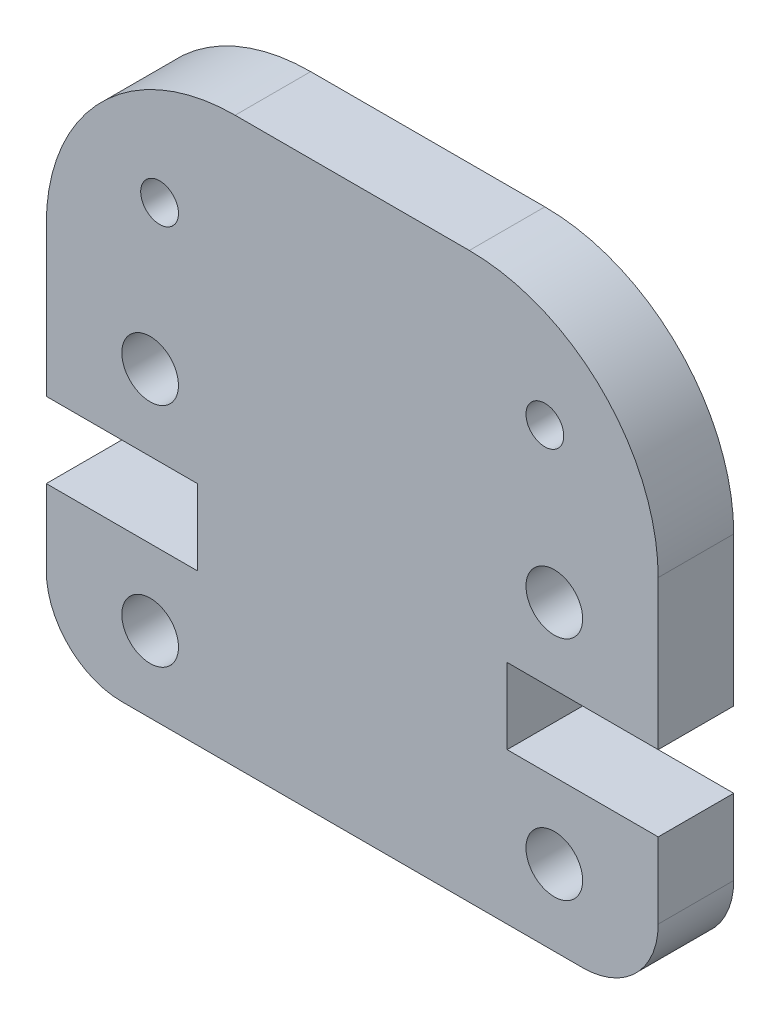
SolidWorks part; units mm, degrees
ref_plane "Front Plane" through (0, 0, 0) normal (0, 0, 1) x (1, 0, 0)
ref_plane "Top Plane" through (0, 0, 0) normal (0, 1, 0) x (1, 0, 0)
ref_plane "Right Plane" through (0, 0, 0) normal (1, 0, 0) x (0, 0, -1)
sketch "Sketch2" plane through (0, 0, 0) normal (0, 0, 1) x (1, 0, 0)
  line L0 (0, 9.945) -> (0, 6)
  line L1 (5, 14.945) -> (11.2, 14.945)
  line L2 (8.1, 14.945) -> (8.1, 0) construction
  line L3 (2, 0) -> (14.2, 0)
  line L4 (12.2, 4) -> (16.2, 4)
  line L5 (12.2, 6) -> (12.2, 4)
  line L6 (16.2, 6) -> (12.2, 6)
  line L7 (16.2, 2) -> (16.2, 4)
  line L8 (16.2, 9.945) -> (16.2, 6)
  line L17 (0, 2) -> (0, 4)
  line L18 (0, 6) -> (4, 6)
  line L20 (4, 6) -> (4, 4)
  line L21 (4, 4) -> (0, 4)
  circle A0 centre (13.45, 8) radius 0.75
  circle A1 centre (13.45, 2) radius 0.75
  arc A2 (16.2, 2) -> (14.2, 0) centre (14.2, 2) cw
  circle A3 centre (13.2, 11.942) radius 0.5
  arc A4 (11.2, 14.945) -> (16.2, 9.945) centre (11.2, 9.945) cw
  arc A11 (5, 14.945) -> (0, 9.945) centre (5, 9.945) ccw
  circle A13 centre (3, 11.942) radius 0.5
  arc A15 (0, 2) -> (2, 0) centre (2, 2) ccw
  circle A17 centre (2.75, 2) radius 0.75
  circle A18 centre (2.75, 8) radius 0.75
  dimension "D1" = 1
  dimension "D2" = 1.5
  dimension "D3" = 5
  dimension "D4" = 2
  dimension "D5" = 3
  dimension "D6" = 8.1
  dimension "D7" = 8
  dimension "D8" = 3.003
  dimension "D9" = 14.945
extrude "Boss-Extrude1" add sketch "Sketch2" along normal blind 2
equation "\"D6@Sketch2\"= \"fingerWidth@parametersSketch@prostheticParameters.SLDPRT\" / 2'Finger width"
equation "\"D9@Sketch2\"= ( ( \"HL@parametersSketch@prostheticParameters.SLDPRT\" * 0.097 ) - 3 ) 'DIP legth-Silicone Sheet DIP"
